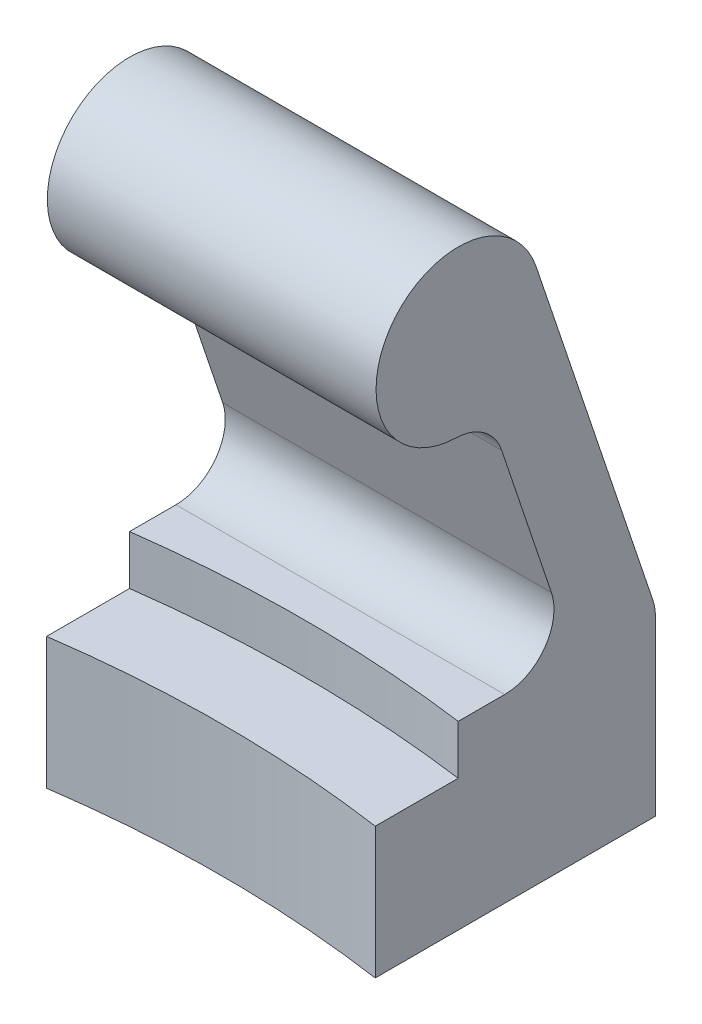
SolidWorks part; units mm, degrees
ref_plane "Front Plane" through (0, 0, 0) normal (0, 0, 1) x (1, 0, 0)
ref_plane "Top Plane" through (0, 0, 0) normal (0, 1, 0) x (1, 0, 0)
ref_plane "Right Plane" through (0, 0, 0) normal (1, 0, 0) x (0, 0, -1)
sketch "Sketch1" plane through (0, 0, 0) normal (0, 1, 0) x (1, 0, 0)
  line L0 (0, 0) -> (0, 75) construction
  line L1 (-10, 69.282) -> (-10, 74.3303)
  line L2 (10, 69.282) -> (10, 74.3303)
  line L3 (-10, 74.3303) -> (-10, 86.3303)
  line L4 (-10, 86.3303) -> (10, 86.3303)
  line L5 (10, 86.3303) -> (10, 74.3303)
  circle A0 centre (0, 0) radius 70 construction
  circle A1 centre (0, 0) radius 75 construction
  arc A2 (-10, 69.282) -> (10, 69.282) centre (0, 0) cw
  arc A3 (-10, 74.3303) -> (10, 74.3303) centre (0, 0) cw construction
  point P10 (0, 70)
  point P12 (3.4451, 75)
  point P15 (6.1121, 69.7326)
  dimension "D1" = 140
  dimension "D2" = 150
  dimension "D3" = 20
  dimension "D4" = 12
extrude "Boss-Extrude1" add sketch "Sketch1" along normal blind 8
sketch "Sketch2" plane through (0, 8, 0) normal (0, 1, 0) x (1, 0, 0)
  line L0 (-10, 86.3303) -> (-10, 69.282) construction
  line L1 (10, 69.282) -> (10, 86.3303) construction
  line L2 (-10, 74.3303) -> (-10, 86.3303)
  line L3 (-10, 86.3303) -> (10, 86.3303)
  line L4 (10, 86.3303) -> (10, 74.3303)
  arc A0 (-10, 74.3303) -> (10, 74.3303) centre (0, 0) cw
  dimension "D1" = 75
extrude "Boss-Extrude2" add sketch "Sketch2" along normal blind 3
sketch "Sketch3" plane through (10, 0, 0) normal (1, 0, 0) x (0, 0, -1)
  line L3 (74.3303, 11) -> (86.3303, 11) construction
  line L4 (81.3303, 11) -> (86.3303, 11)
  line L5 (74.3303, 31) -> (86.3303, 31) construction
  line L6 (86.3303, 31) -> (86.3303, 11) construction
  line L8 (86.3303, 11) -> (79.0696, 32.5936)
  line L9 (76.1689, 26.3503) -> (81.3303, 11)
  circle A3 centre (74.3303, 31) radius 5 construction
  arc A4 (76.1689, 26.3503) -> (79.0696, 32.5936) centre (74.3303, 31) cw
  dimension "D4" = 10
  dimension "D1" = 5
  dimension "D2" = 12
  dimension "D3" = 20
extrude "Boss-Extrude3" add sketch "Sketch3" against normal up to surface (20 mm away) up to face at (-10, 6.3333, -76.6476)
fillet "Fillet5" radius 3 3 edges at (0, 26.3503, -76.1689) (0, 11, -81.3303) (0, 11, -86.3303)
